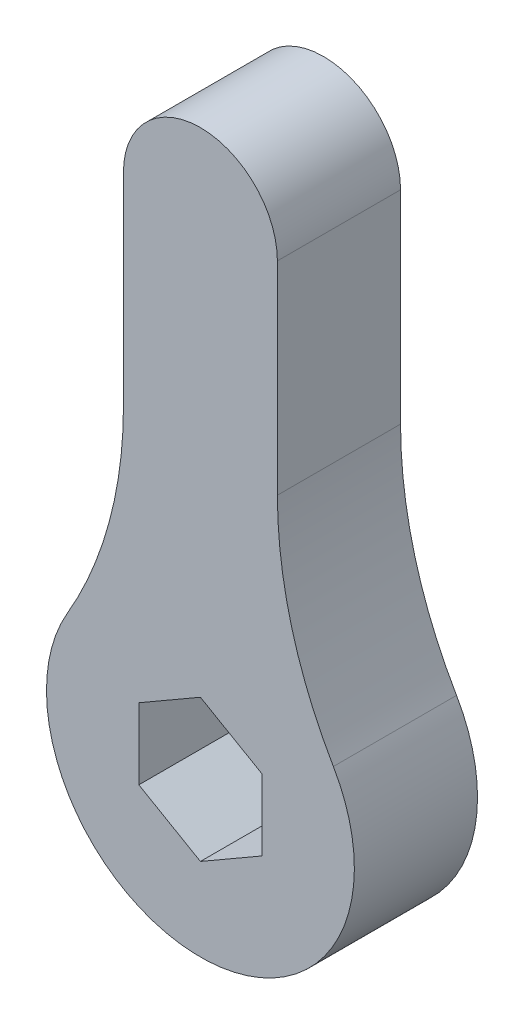
SolidWorks part; units mm, degrees
ref_plane "Front" through (0, 0, 0) normal (0, 0, 1) x (1, 0, 0)
ref_plane "Top" through (0, 0, 0) normal (0, 1, 0) x (1, 0, 0)
ref_plane "Right" through (0, 0, 0) normal (1, 0, 0) x (0, 0, -1)
sketch "Sketch1" plane through (0, 0, 0) normal (0, 0, 1) x (1, 0, 0)
  line L1 (0, 3.4641) -> (-3, 1.7321)
  line L2 (-3, 1.7321) -> (-3, -1.7321)
  line L3 (-3, -1.7321) -> (0, -3.4641)
  line L4 (0, -3.4641) -> (3, -1.7321)
  line L5 (3, -1.7321) -> (3, 1.7321)
  line L6 (3, 1.7321) -> (0, 3.4641)
  line L8 (-3.75, 13.8632) -> (-3.75, 23.75)
  line L10 (3.75, 13.8632) -> (3.75, 23.75)
  arc A0 (-6.4773, 3.7809) -> (6.4773, 3.7809) centre (0, 0) ccw
  circle A1 centre (0, 0) radius 3 construction
  arc A2 (-3.75, 23.75) -> (3.75, 23.75) centre (0, 23.75) cw
  arc A3 (3.75, 13.8632) -> (6.4773, 3.7809) centre (23.75, 13.8632) ccw
  arc A4 (-3.75, 13.8632) -> (-6.4773, 3.7809) centre (-23.75, 13.8632) cw
  point P1 (0, 0)
  point P19 (0, 27.5)
  point P20 (0, -7.5)
  dimension "D2" = 20
  dimension "D3" = 7.5
  dimension "D5" = 35
  dimension "D1" = 6
  dimension "D4" = 7.5
extrude "Boss-Extrude1" add sketch "Sketch1" along normal blind 6
